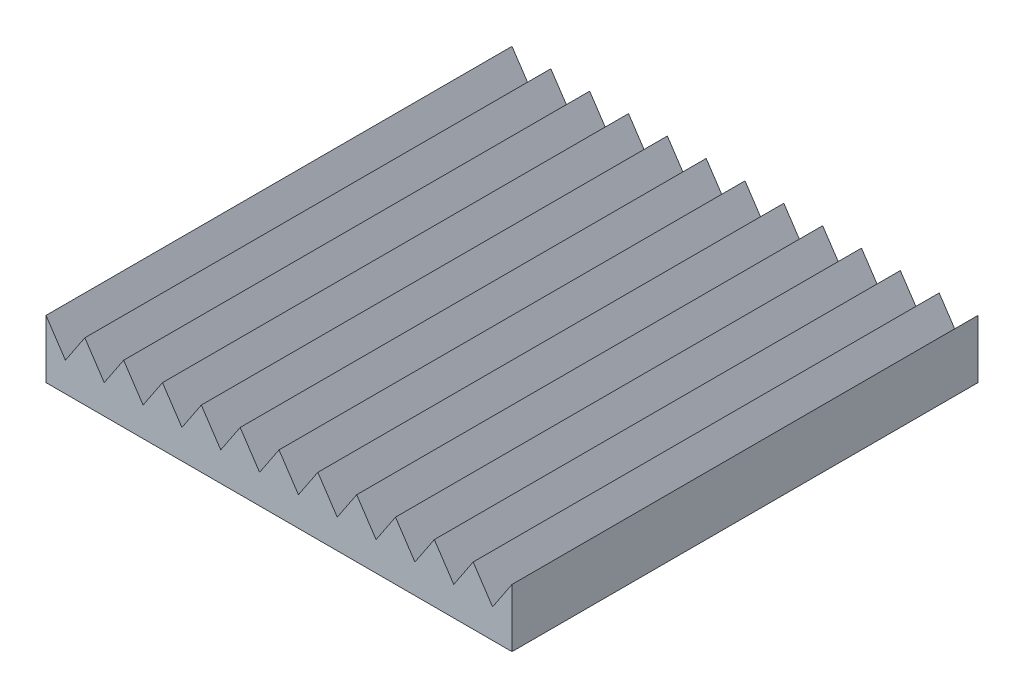
SolidWorks part; units mm, degrees
ref_plane "Front Plane" through (0, 0, 0) normal (0, 0, 1) x (1, 0, 0)
ref_plane "Top Plane" through (0, 0, 0) normal (0, 1, 0) x (1, 0, 0)
ref_plane "Right Plane" through (0, 0, 0) normal (1, 0, 0) x (0, 0, -1)
sketch "Sketch1" plane through (0, 0, 0) normal (0, 1, 0) x (1, 0, 0)
  line L1 (0, 0) -> (304.8, 0)
  line L2 (0, 0) -> (0, -304.8)
  line L3 (0, -304.8) -> (304.8, -304.8)
  line L4 (304.8, 0) -> (304.8, -304.8)
extrude "Boss-Extrude1" add sketch "Sketch1" along normal blind 38.1
sketch "Sketch2" plane through (0, 0, 304.8) normal (0, 0, 1) x (1, 0, 0)
  line L0 (0, 19.05) -> (304.8, 19.05) construction
  line L1 (0, 38.1) -> (0, 0) construction
  line L2 (304.8, 38.1) -> (304.8, 0) construction
  line L3 (0, 38.1) -> (12.7, 19.05)
  line L4 (12.7, 19.05) -> (25.4, 38.1)
  line L5 (0, 38.1) -> (304.8, 38.1) construction
  line L6 (0, 38.1) -> (25.4, 38.1)
extrude "Cut-Extrude1" cut sketch "Sketch2" against normal through all
pattern_linear "LPattern1" count 12 spacing 25.4 along (1, 0, 0) of "Cut-Extrude1"
